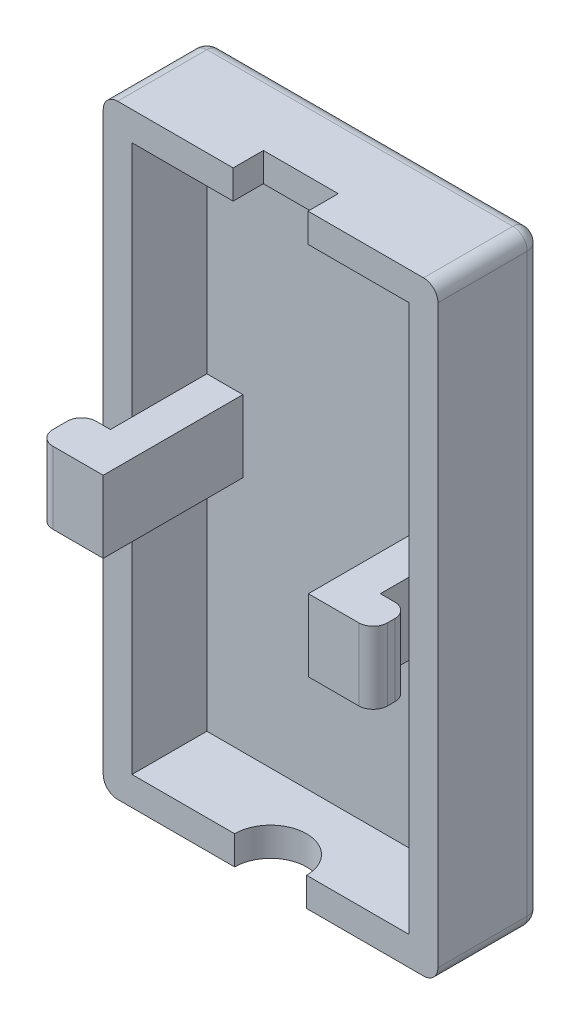
SolidWorks part; units mm, degrees
ref_plane "Front Plane" through (0, 0, 0) normal (0, 0, 1) x (1, 0, 0)
ref_plane "Top Plane" through (0, 0, 0) normal (0, 1, 0) x (1, 0, 0)
ref_plane "Right Plane" through (0, 0, 0) normal (1, 0, 0) x (0, 0, -1)
sketch "Sketch1" plane through (0, 0, 0) normal (0, 0, 1) x (1, 0, 0)
  line L1 (-11.625, 21) -> (11.625, 21)
  line L2 (-11.625, 21) -> (-11.625, -21)
  line L3 (-11.625, -21) -> (11.625, -21)
  line L4 (11.625, 21) -> (11.625, -21)
  line L5 (-11.625, 21) -> (11.625, -21) construction
  line L6 (-11.625, -21) -> (11.625, 21) construction
  point P0 (0, 0)
  dimension "D1" = 23.25
  dimension "D2" = 42
extrude "Boss-Extrude1" add sketch "Sketch1" along normal blind 2
sketch "Sketch2" plane through (0, 0, 2) normal (0, 0, 1) x (1, 0, 0)
  line L1 (-11.625, 21) -> (11.625, 21)
  line L2 (-11.625, 21) -> (-11.625, -21)
  line L3 (-11.625, -21) -> (11.625, -21)
  line L4 (11.625, 21) -> (11.625, -21)
  line L5 (-9.625, 19) -> (9.625, 19)
  line L6 (-9.625, 19) -> (-9.625, -19)
  line L7 (-9.625, -19) -> (9.625, -19)
  line L8 (9.625, 19) -> (9.625, -19)
  dimension "D1" = 2
  dimension "D2" = 2
  dimension "D3" = 2
  dimension "D4" = 2
extrude "Boss-Extrude2" add sketch "Sketch2" along normal blind 5.2
sketch "Sketch3" plane through (0, -19, 0) normal (0, 1, 0) x (1, 0, 0)
  line L0 (11.625, -7.2) -> (-11.625, -7.2) construction
  line L1 (-2.5, -7.2) -> (2.5, -7.2)
  arc A0 (2.5, -7.2) -> (-2.5, -7.2) centre (0, -7.2) ccw
  dimension "D1" = 5
extrude "Cut-Extrude1" cut sketch "Sketch3" against normal through all
sketch "Sketch4" plane through (0, 19, 0) normal (0, -1, 0) x (1, 0, 0)
  line L0 (9.625, 7.2) -> (-9.625, 7.2) construction
  line L1 (-2.6, 9.3) -> (2.6, 9.3)
  line L2 (-2.6, 9.3) -> (-2.6, 5.1)
  line L3 (-2.6, 5.1) -> (2.6, 5.1)
  line L4 (2.6, 9.3) -> (2.6, 5.1)
  line L5 (-2.6, 9.3) -> (2.6, 5.1) construction
  line L6 (-2.6, 5.1) -> (2.6, 9.3) construction
  point P0 (0, 7.2)
  dimension "D1" = 4.2
  dimension "D2" = 5.2
extrude "Cut-Extrude2" cut sketch "Sketch4" against normal through all
sketch "Sketch5" plane through (9.625, 0, 0) normal (-1, 0, 0) x (0, 0, 1)
  line L0 (2, 2.5) -> (0, 2.5)
  line L2 (0, 2.5) -> (0, -2.5)
  line L5 (4.5, 2.5) -> (2, 2.5)
  line L9 (4.5, -2.5) -> (2, -2.5)
  line L11 (0, -2.5) -> (2, -2.5)
  line L15 (4.5, 2.5) -> (7.2, 2.5)
  line L16 (7.2, -19) -> (7.2, 19) construction
  line L17 (7.2, 2.5) -> (11.7, 2.5)
  line L18 (11.7, 2.5) -> (11.7, -2.5)
  line L19 (11.7, -2.5) -> (4.5, -2.5)
  line L20 (0, 0) -> (7.2, 0)
  line L21 (7.2, 21) -> (7.2, -21) construction
  line M7 (2, 19) -> (2, -19)
  line M9 (7.2, -19) -> (7.2, 19)
  dimension "D1" = 4.5
  dimension "D2" = 2.5
extrude "Boss-Extrude3" add sketch "Sketch5" along normal blind 2.5 contours L19 L18 L17 M9 | L20 L15 L5 M7 M9 | L20 L9 L19 M7 M9 | L20 L2 L11 M7 | L2 L20 L0 M7
sketch "Sketch6" plane through (-9.625, 0, 0) normal (1, 0, 0) x (0, 0, -1)
  line L0 (-11.7, -2.5) -> (-2, -2.5)
  line L1 (-7.2, 19) -> (-7.2, -19) construction
  line L2 (-2, 19) -> (-2, -19) construction
  line L3 (-2, 0) -> (-2, 2.5)
  line L4 (-2, -0.2697) -> (-2, -2.5)
  line L7 (-7.2, 2.5) -> (-2, 2.5)
  line L9 (-11.7, -2.5) -> (-11.7, 2.5)
  line L10 (-11.7, 2.5) -> (-7.2, 2.5)
  line L13 (-2, -19) -> (-2, 19)
  line L14 (-2, 19) -> (-7.2, 19)
  line L15 (-7.2, 19) -> (-7.2, -19)
  line L16 (-7.2, -19) -> (-2, -19)
  line L17 (-2, -0.2697) -> (-2, 0)
  dimension "D1" = 2.5
  dimension "D4" = 0
extrude "Boss-Extrude4" add sketch "Sketch6" along normal blind 2.5
sketch "Sketch7" plane through (-9.625, 0, 0) normal (-1, 0, 0) x (0, 0, 1)
  line L1 (11.7, 2.5) -> (8.7, 2.5)
  line L2 (11.7, 2.5) -> (11.7, -2.5)
  line L4 (8.7, 2.5) -> (8.7, -2.5247)
  line L5 (8.7, -2.5247) -> (11.7, -2.5)
  dimension "D1" = 3
extrude "Boss-Extrude5" add sketch "Sketch7" along normal blind 2
sketch "Sketch8" plane through (9.625, 0, 0) normal (1, 0, 0) x (0, 0, -1)
  line L6 (-11.7, 2.5) -> (-9.2, 2.5)
  line L7 (-11.7, 2.5) -> (-11.7, -2.5)
  line L8 (-11.7, -2.5) -> (-9.2, -2.5)
  line L9 (-9.2, 2.5) -> (-9.2, -2.5)
  dimension "D1" = 2.5
extrude "Boss-Extrude6" add sketch "Sketch8" along normal blind 2
fillet "Fillet1" radius 1 4 edges at (-11.625, -0.0124, 8.7) (-11.625, 0, 11.7) (11.625, 0, 9.2) (11.625, 0, 11.7)
fillet "Fillet2" radius 1 8 edges at (11.625, -21, 3.6) (0, -21, 0) (-11.625, -21, 3.6) (-11.625, 0, 0) (-11.625, 21, 3.6) (0, 21, 0) (11.625, 0, 0) (11.625, 21, 3.6)
sketch "Sketch11" plane through (0, 0, 0) normal (0, 0, -1) x (-1, 0, 0)
  text T0 "LUX detector" font "Centaur" height in points 8
extrude "Cut-Extrude4" cut sketch "Sketch11" against normal blind 1
sketch "Sketch12" plane through (0, 0, 0) normal (0, 0, -1) x (-1, 0, 0)
  text T0 "Meritus" font "Book Antiqua" height in points 8
extrude "Cut-Extrude5" cut sketch "Sketch12" against normal blind 1
